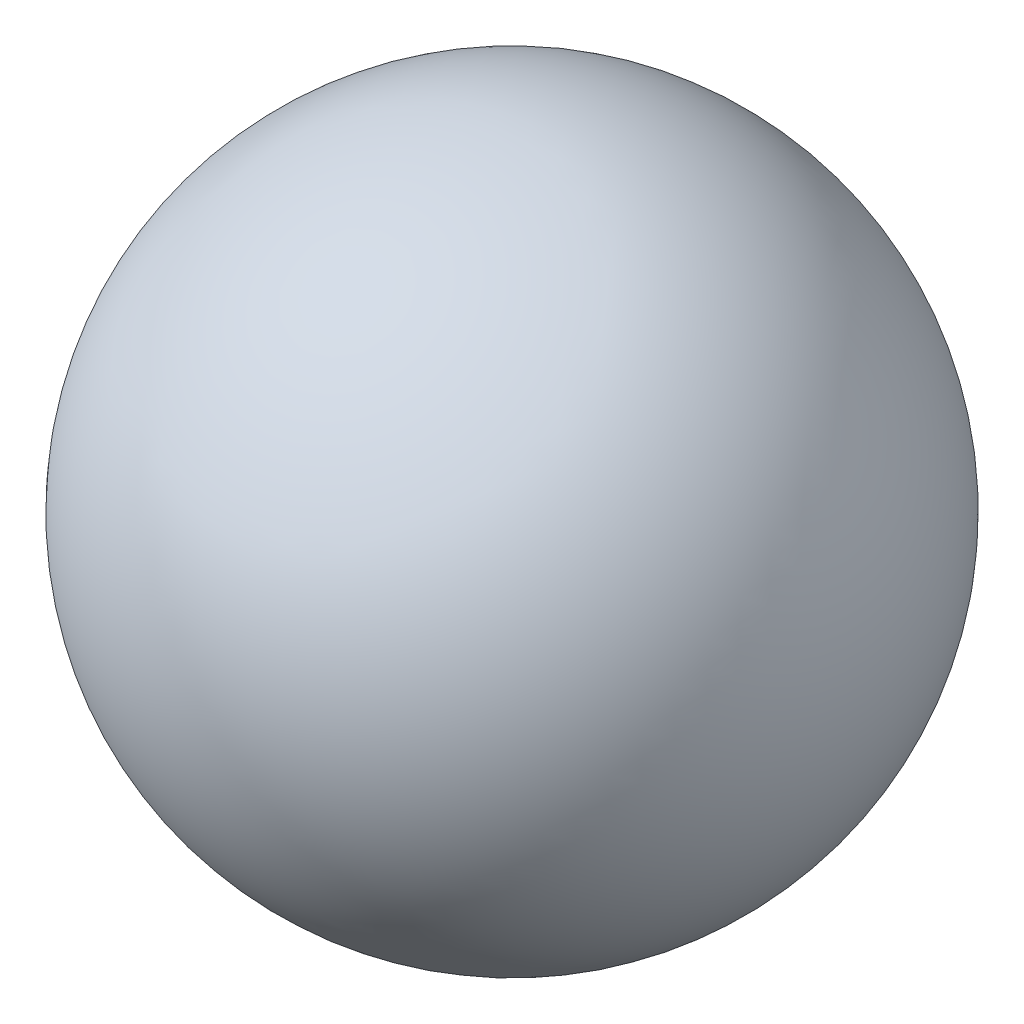
SolidWorks part; units mm, degrees
ref_plane "Front Plane" through (0, 0, 0) normal (0, 0, 1) x (1, 0, 0)
ref_plane "Top Plane" through (0, 0, 0) normal (0, 1, 0) x (1, 0, 0)
ref_plane "Right Plane" through (0, 0, 0) normal (1, 0, 0) x (0, 0, -1)
sketch "Sketch2" plane through (0, 0, 0) normal (0, 1, 0) x (1, 0, 0)
  line L0 (0, 0) -> (-35.4706, -27.8698) construction
  circle A0 centre (0, 0) radius 31.75
revolve "Revolve4" add sketch "Sketch2" angle 360 about L0
